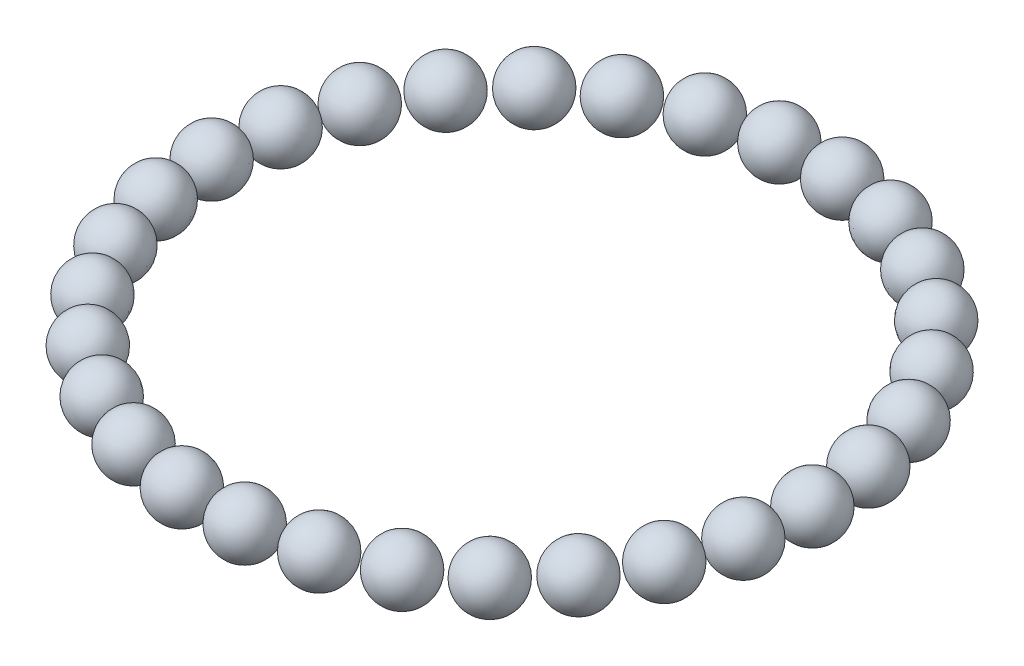
SolidWorks part; units mm, degrees
ref_plane "Front Plane" through (0, 0, 0) normal (0, 0, 1) x (1, 0, 0)
ref_plane "Top Plane" through (0, 0, 0) normal (0, 1, 0) x (1, 0, 0)
ref_plane "Right Plane" through (0, 0, 0) normal (1, 0, 0) x (0, 0, -1)
sketch "Sketch1" plane through (0, 0, 0) normal (0, 0, 1) x (1, 0, 0)
  line L0 (0, 1.25) -> (0, -1.25) construction
  line L1 (0, 1.25) -> (0, -1.25)
  arc A0 (0, -1.25) -> (0, 1.25) centre (0, 0) ccw
  dimension "D1" = 1.25
revolve "Revolve1" add sketch "Sketch1" angle 360 about L0
sketch "Sketch2" plane through (0, 0, 0) normal (0, 0, 1) x (1, 0, 0)
  line L0 (-1.25, 0) -> (12.7, 0)
  line L1 (12.7, 0) -> (12.7, 2.32) construction
  circle A0 centre (0, 0) radius 1.25 construction
  dimension "D1" = 13.95
pattern_circular "CirPattern2" count 30 over 360 about axis through (12.7, 0, 0) along (0, 1, 0) of bodies 101
